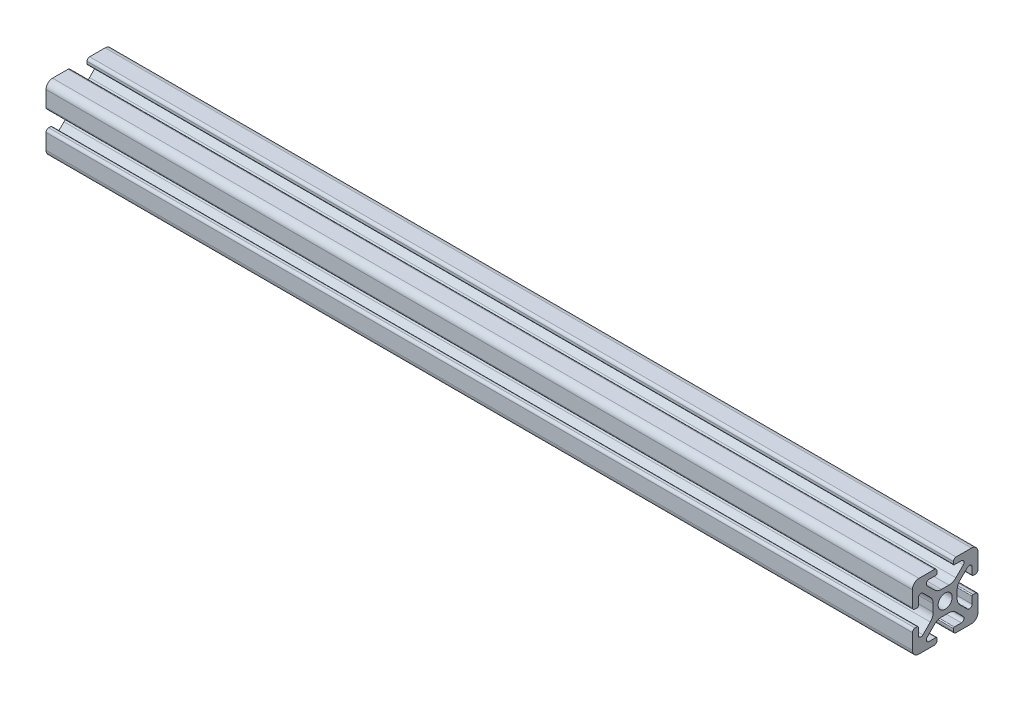
SolidWorks part; units mm, degrees
material "1060 Legierung"
material "1060 Legierung"
ref_plane "Ebene vorne" through (0, 0, 0) normal (0, 0, 1) x (1, 0, 0)
ref_plane "Ebene oben" through (0, 0, 0) normal (0, 1, 0) x (1, 0, 0)
ref_plane "Ebene rechts" through (0, 0, 0) normal (1, 0, 0) x (0, 0, -1)
sketch "Skizze1" plane through (0, 0, 0) normal (0, 1, 0) x (1, 0, 0)
  line L0 (-132, 0) -> (132, 0)
  dimension "D1" = 264
other "Quadratisch 20X20(1)"
ref_plane "Ebene1" through (-132, 0, 0) normal (1, 0, 0) x (0, 0, -1)
sketch "Skizze11" plane through (-132, 0, 0) normal (1, 0, 0) x (0, 0, -1)
  line L0 (3.3, -10) -> (8, -10)
  line L1 (10, -8) -> (10, -3.3)
  line L2 (9.2, -2.5) -> (8.5, -2.5)
  line L3 (8.2, -2.8) -> (8.2, -4.9176)
  line L4 (6.779, -5.5062) -> (4.5287, -3.2559)
  line L5 (3.65, -1.1346) -> (3.65, 1.1346)
  line L6 (4.5287, 3.2559) -> (6.779, 5.5062)
  line L7 (8.2, 4.9176) -> (8.2, 2.8)
  line L8 (8.5, 2.5) -> (9.2, 2.5)
  line L9 (10, 3.3) -> (10, 8)
  line L10 (8, 10) -> (3.3, 10)
  line L11 (2.5, 9.2) -> (2.5, 8.5)
  line L12 (2.8, 8.2) -> (4.9176, 8.2)
  line L13 (5.5062, 6.779) -> (3.2559, 4.5287)
  line L14 (1.1346, 3.65) -> (-1.1346, 3.65)
  line L15 (-3.2559, 4.5287) -> (-5.5062, 6.779)
  line L16 (-4.9176, 8.2) -> (-2.8, 8.2)
  line L17 (-2.5, 8.5) -> (-2.5, 9.2)
  line L18 (-3.3, 10) -> (-8, 10)
  line L19 (-10, 8) -> (-10, 3.3)
  line L20 (-9.2, 2.5) -> (-8.5, 2.5)
  line L21 (-8.2, 2.8) -> (-8.2, 4.9176)
  line L22 (-6.779, 5.5062) -> (-4.5287, 3.2559)
  line L23 (-3.65, 1.1346) -> (-3.65, -1.1346)
  line L24 (-4.5287, -3.2559) -> (-6.779, -5.5062)
  line L25 (-8.2, -4.9176) -> (-8.2, -2.8)
  line L26 (-8.5, -2.5) -> (-9.2, -2.5)
  line L27 (-10, -3.3) -> (-10, -8)
  line L28 (-8, -10) -> (-3.3, -10)
  line L29 (-2.5, -9.2) -> (-2.5, -8.5)
  line L30 (-2.8, -8.2) -> (-4.9176, -8.2)
  line L31 (-5.5062, -6.779) -> (-3.2559, -4.5287)
  line L32 (-1.1346, -3.65) -> (1.1346, -3.65)
  line L33 (3.2559, -4.5287) -> (5.5062, -6.779)
  line L34 (4.9176, -8.2) -> (2.8, -8.2)
  line L35 (2.5, -8.5) -> (2.5, -9.2)
  circle A0 centre (0, 0) radius 2.15
  arc A1 (2.5, -9.2) -> (3.3, -10) centre (3.3, -9.2) ccw
  arc A2 (8, -10) -> (10, -8) centre (8, -8) ccw
  arc A3 (10, -3.3) -> (9.2, -2.5) centre (9.2, -3.3) ccw
  arc A4 (8.5, -2.5) -> (8.2, -2.8) centre (8.5, -2.8) ccw
  arc A5 (8.2, -4.9176) -> (6.779, -5.5062) centre (7.3676, -4.9176) cw
  arc A6 (4.5287, -3.2559) -> (3.65, -1.1346) centre (6.65, -1.1346) cw
  arc A7 (3.65, 1.1346) -> (4.5287, 3.2559) centre (6.65, 1.1346) cw
  arc A8 (6.779, 5.5062) -> (8.2, 4.9176) centre (7.3676, 4.9176) cw
  arc A9 (8.2, 2.8) -> (8.5, 2.5) centre (8.5, 2.8) ccw
  arc A10 (9.2, 2.5) -> (10, 3.3) centre (9.2, 3.3) ccw
  arc A11 (10, 8) -> (8, 10) centre (8, 8) ccw
  arc A12 (3.3, 10) -> (2.5, 9.2) centre (3.3, 9.2) ccw
  arc A13 (2.5, 8.5) -> (2.8, 8.2) centre (2.8, 8.5) ccw
  arc A14 (4.9176, 8.2) -> (5.5062, 6.779) centre (4.9176, 7.3676) cw
  arc A15 (3.2559, 4.5287) -> (1.1346, 3.65) centre (1.1346, 6.65) cw
  arc A16 (-1.1346, 3.65) -> (-3.2559, 4.5287) centre (-1.1346, 6.65) cw
  arc A17 (-5.5062, 6.779) -> (-4.9176, 8.2) centre (-4.9176, 7.3676) cw
  arc A18 (-2.8, 8.2) -> (-2.5, 8.5) centre (-2.8, 8.5) ccw
  arc A19 (-2.5, 9.2) -> (-3.3, 10) centre (-3.3, 9.2) ccw
  arc A20 (-8, 10) -> (-10, 8) centre (-8, 8) ccw
  arc A21 (-10, 3.3) -> (-9.2, 2.5) centre (-9.2, 3.3) ccw
  arc A22 (-8.5, 2.5) -> (-8.2, 2.8) centre (-8.5, 2.8) ccw
  arc A23 (-8.2, 4.9176) -> (-6.779, 5.5062) centre (-7.3676, 4.9176) cw
  arc A24 (-4.5287, 3.2559) -> (-3.65, 1.1346) centre (-6.65, 1.1346) cw
  arc A25 (-3.65, -1.1346) -> (-4.5287, -3.2559) centre (-6.65, -1.1346) cw
  arc A26 (-6.779, -5.5062) -> (-8.2, -4.9176) centre (-7.3676, -4.9176) cw
  arc A27 (-8.2, -2.8) -> (-8.5, -2.5) centre (-8.5, -2.8) ccw
  arc A28 (-9.2, -2.5) -> (-10, -3.3) centre (-9.2, -3.3) ccw
  arc A29 (-10, -8) -> (-8, -10) centre (-8, -8) ccw
  arc A30 (-3.3, -10) -> (-2.5, -9.2) centre (-3.3, -9.2) ccw
  arc A31 (-2.5, -8.5) -> (-2.8, -8.2) centre (-2.8, -8.5) ccw
  arc A32 (-4.9176, -8.2) -> (-5.5062, -6.779) centre (-4.9176, -7.3676) cw
  arc A33 (-3.2559, -4.5287) -> (-1.1346, -3.65) centre (-1.1346, -6.65) cw
  arc A34 (1.1346, -3.65) -> (3.2559, -4.5287) centre (1.1346, -6.65) cw
  arc A35 (5.5062, -6.779) -> (4.9176, -8.2) centre (4.9176, -7.3676) cw
  arc A36 (2.8, -8.2) -> (2.5, -8.5) centre (2.8, -8.5) ccw
  point P110 (0, 0)
